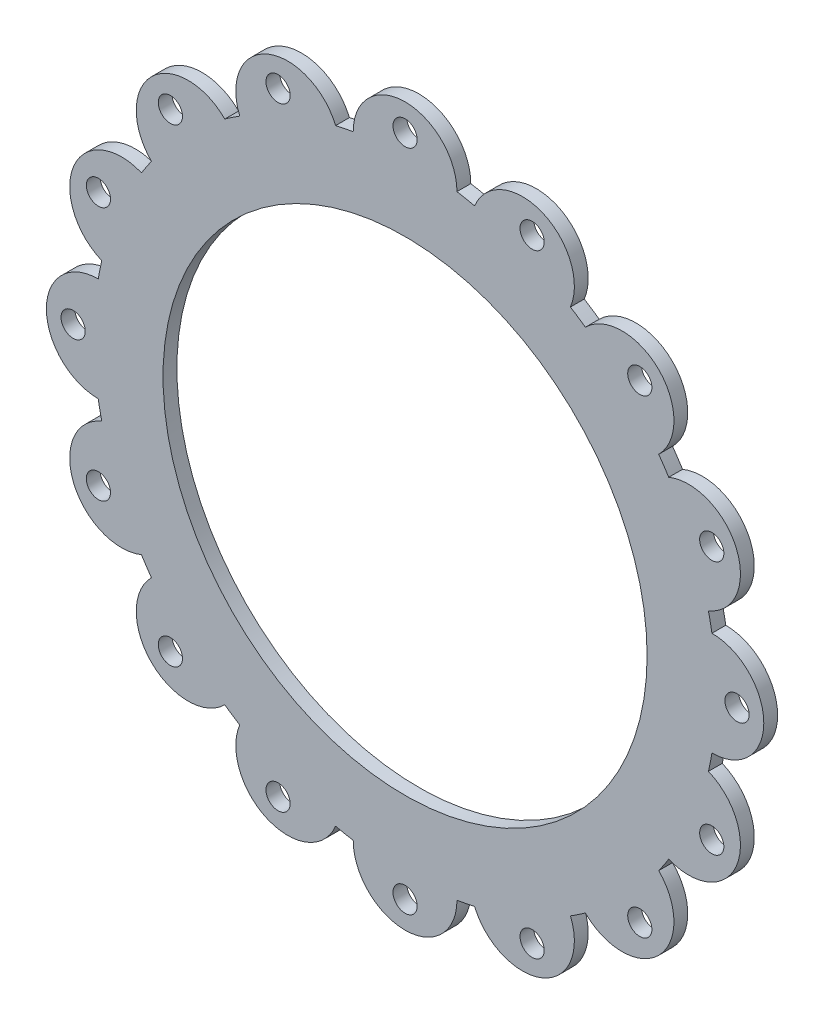
SolidWorks part; units mm, degrees
ref_plane "Front Plane" through (0, 0, 0) normal (0, 0, 1) x (1, 0, 0)
ref_plane "Top Plane" through (0, 0, 0) normal (0, 1, 0) x (1, 0, 0)
ref_plane "Right Plane" through (0, 0, 0) normal (1, 0, 0) x (0, 0, -1)
sketch "Sketch1" plane through (0, 0, 0) normal (0, 0, 1) x (1, 0, 0)
  circle A0 centre (0, 0) radius 35
  circle A1 centre (0, 0) radius 45
  dimension "D1" = 70
  dimension "D2" = 10
extrude "Boss-Extrude1" add sketch "Sketch1" along normal blind 2
sketch "Sketch2" plane through (0, 0, 0) normal (0, 0, 1) x (1, 0, 0)
  line L0 (-7.5, 44.3706) -> (7.5, 44.3706) construction
  line L1 (0, 48) -> (0, 0) construction
  circle A0 centre (0, 0) radius 45 construction
  arc A1 (7.5, 44.3706) -> (-7.5, 44.3706) centre (0, 0) ccw
  arc A2 (-7.5, 44.3706) -> (7.5, 44.3706) centre (0, 44.3706) cw
  circle A3 centre (0, 48) radius 1.75
  point P6 (3.0493, 44.8966)
  dimension "D3" = 3.5
  dimension "D1" = 15
  dimension "D2" = 48
extrude "Boss-Extrude2" add sketch "Sketch2" along normal blind 2
pattern_circular "CirPattern1" count 16 over 360 about axis through (0, 0, 0) along (0, 0, 1) of "Boss-Extrude2"
